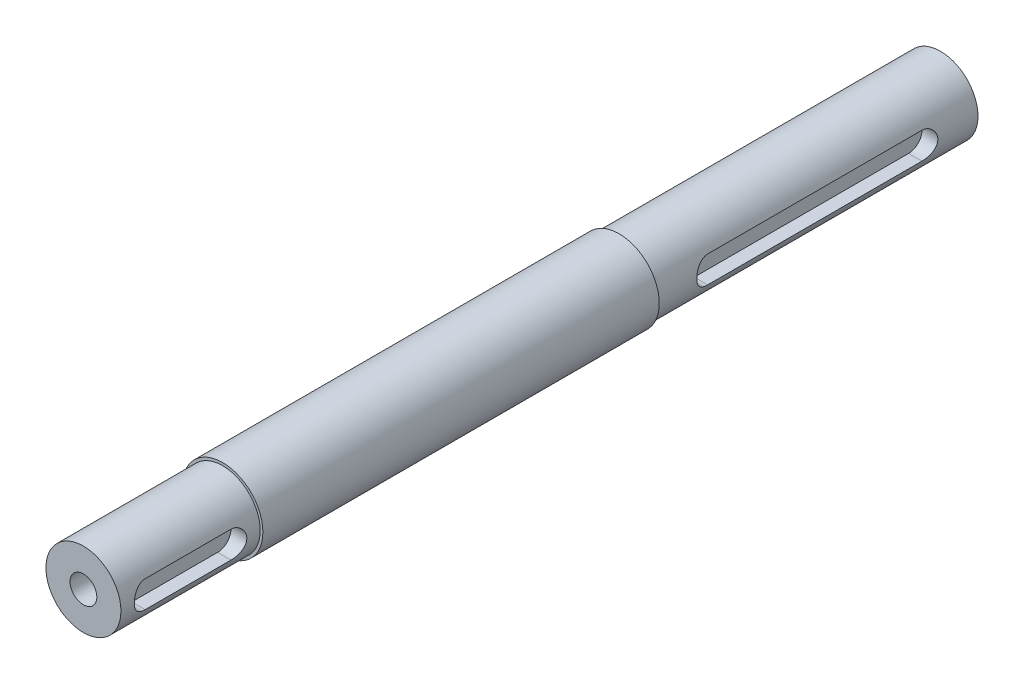
SolidWorks part; units mm, degrees
ref_plane "Plan de face" through (0, 0, 0) normal (0, 0, 1) x (1, 0, 0)
ref_plane "Plan de dessus" through (0, 0, 0) normal (0, 1, 0) x (1, 0, 0)
ref_plane "Plan de droite" through (0, 0, 0) normal (1, 0, 0) x (0, 0, -1)
sketch "Esquisse1" plane through (0, 0, 0) normal (0, 0, 1) x (1, 0, 0)
  circle A0 centre (0, 0) radius 7
  dimension "D1" = 14
extrude "Boss.-Extru.1" add sketch "Esquisse1" along normal blind 60
sketch "Esquisse3" plane through (0, 0, 60) normal (0, 0, 1) x (1, 0, 0)
  circle A0 centre (0, 0) radius 7.5
  dimension "D1" = 15
extrude "Boss.-Extru.2" add sketch "Esquisse3" along normal blind 62
sketch "Esquisse4" plane through (0, 0, 122) normal (0, 0, 1) x (1, 0, 0)
  circle A0 centre (0, 0) radius 7.5
extrude "Boss.-Extru.3" add sketch "Esquisse4" along normal blind 12
sketch "Esquisse5" plane through (0, 0, 134) normal (0, 0, 1) x (1, 0, 0)
  circle A0 centre (0, 0) radius 7
  dimension "D1" = 14
extrude "Boss.-Extru.4" add sketch "Esquisse5" along normal blind 26
ref_plane "Plan1" through (7, 0, 0) normal (1, 0, 0) x (0, 0, -1)
sketch "Esquisse7" plane through (7, 0, 0) normal (1, 0, 0) x (0, 0, -1)
  line L0 (-155, 0) -> (-139, 0) construction
  line L1 (-155, 2.5) -> (-139, 2.5)
  line L2 (-155, -2.5) -> (-139, -2.5)
  line L3 (-160, 7) -> (-160, -7) construction
  arc A0 (-155, 2.5) -> (-155, -2.5) centre (-155, 0) ccw
  arc A1 (-139, -2.5) -> (-139, 2.5) centre (-139, 0) ccw
  point P3 (-147, 0)
  dimension "D1" = 5
  dimension "D2" = 16
  dimension "D3" = 5
extrude "Enlèv. mat.-Extru.1" cut sketch "Esquisse7" against normal blind 2.96
sketch "Esquisse8" plane through (7, 0, 0) normal (1, 0, 0) x (0, 0, -1)
  line L0 (-10, 0) -> (-50, 0) construction
  line L1 (-10, -2.5) -> (-50, -2.5)
  line L2 (-10, 2.5) -> (-50, 2.5)
  line L3 (0, -7) -> (0, 7) construction
  line L4 (-60, -7) -> (-60, 7) construction
  arc A0 (-10, -2.5) -> (-10, 2.5) centre (-10, 0) ccw
  arc A1 (-50, 2.5) -> (-50, -2.5) centre (-50, 0) ccw
  point P3 (-30, 0)
  dimension "D1" = 10
  dimension "D2" = 10
extrude "Enlèv. mat.-Extru.2" cut sketch "Esquisse8" against normal blind 2.96
hole_wizard "Trou pour taraudage pour trou taraudé M61" positions "Esquisse10" profile "Esquisse9" hole size "M6" standard "ISO"
sketch "Esquisse10" plane through (0, 0, 0) normal (0, 0, -1) x (-1, 0, 0)
  point P0 (0, 0)
sketch "Esquisse9" plane through (0, 0, 0) normal (1, 0, 0) x (0, 1, 0)
  line L0 (0, 0) -> (0, 16.5022)
  line L1 (0, 16.5022) -> (2.5, 15)
  line L2 (2.5, 15) -> (2.5, 0)
  line L5 (2.5, 0) -> (0, 0)
  line L10 (0, 16.5022) -> (-2.5, 15) construction
  line L11 (0, -6.35) -> (0, 107.95) construction
  dimension "Diamètre du perçage" = 5
  dimension "Profondeur du perçage" = 15
  dimension "Angle de pointe" = 118
hole_wizard "Trou pour taraudage pour trou taraudé M62" positions "Esquisse12" profile "Esquisse11" hole size "M6" standard "ISO"
sketch "Esquisse12" plane through (0, 0, 160) normal (0, 0, 1) x (1, 0, 0)
  point P0 (0, 0)
sketch "Esquisse11" plane through (0, 0, 160) normal (1, 0, 0) x (0, -1, 0)
  line L0 (0, 0) -> (0, 16.5022)
  line L1 (0, 16.5022) -> (2.5, 15)
  line L2 (2.5, 15) -> (2.5, 0)
  line L5 (2.5, 0) -> (0, 0)
  line L10 (0, 16.5022) -> (-2.5, 15) construction
  line L11 (0, -6.35) -> (0, 107.95) construction
  dimension "Diamètre du perçage" = 5
  dimension "Profondeur du perçage" = 15
  dimension "Angle de pointe" = 118
